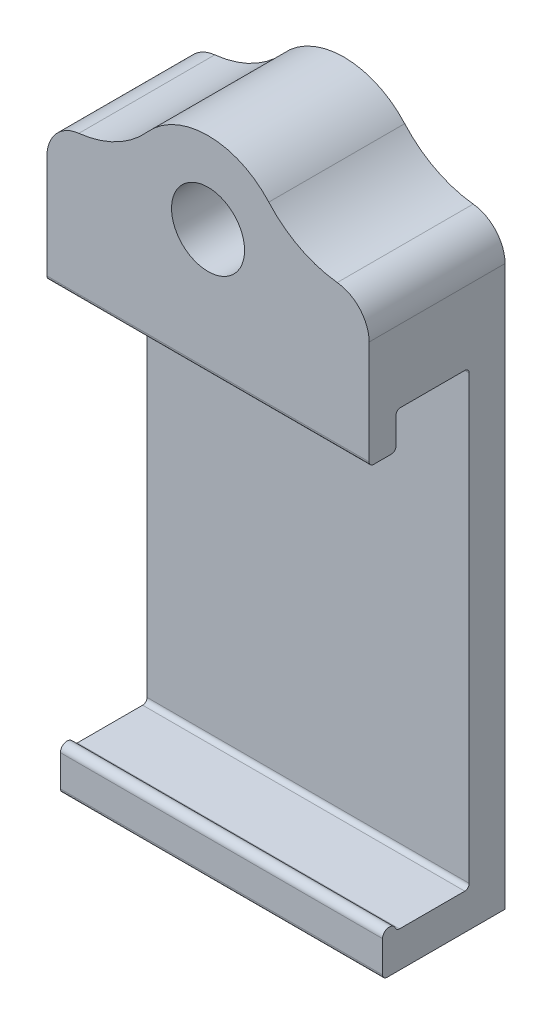
SolidWorks part; units mm, degrees
ref_plane "Front Plane" through (0, 0, 0) normal (0, 0, 1) x (1, 0, 0)
ref_plane "Top Plane" through (0, 0, 0) normal (0, 1, 0) x (1, 0, 0)
ref_plane "Right Plane" through (0, 0, 0) normal (1, 0, 0) x (0, 0, -1)
sketch "Sketch2" plane through (0, 0, 0) normal (1, 0, 0) x (0, 0, -1)
  line L0 (-3.25, 16.825) -> (-5.6312, 16.825)
  line L1 (-3.25, -20) -> (3.25, -20) construction
  line L2 (-3.25, -20) -> (-3.25, 20) construction
  line L3 (-3.25, 20) -> (3.25, 20) construction
  line L4 (3.25, -20) -> (3.25, 20) construction
  line L5 (-3.25, -20) -> (3.25, 20) construction
  line L6 (-3.25, 20) -> (3.25, -20) construction
  line L7 (-5.6312, 16.825) -> (-5.6312, 23.175)
  line L8 (-5.6312, 23.175) -> (6.425, 23.175)
  line L9 (6.425, 23.175) -> (6.425, -23.175)
  line L10 (6.425, -23.175) -> (-4.4406, -23.175)
  line L11 (-4.4406, -23.175) -> (-4.4406, -20)
  line L12 (-3.25, 16.825) -> (-3.25, 20)
  line L13 (-3.25, 20) -> (3.25, 20)
  line L14 (3.25, 20) -> (3.25, -20)
  line L15 (3.25, -20) -> (-3.25, -20)
  line L16 (-4.4406, -20) -> (-3.25, -20) construction
  line L17 (-5.6312, 23.175) -> (-3.25, 20) construction
  line L18 (3.25, 20) -> (6.425, 23.175) construction
  line L19 (3.25, -20) -> (6.425, -23.175) construction
  arc A0 (-3.25, -20) -> (-4.4406, -20) centre (-3.8453, -20) ccw
  point P0 (0, 0)
  dimension "D3" = 0.5953
  dimension "D1" = 40
  dimension "D2" = 6.5
  dimension "D4" = 3.175
  dimension "D5" = 2.3813
  dimension "D6" = 3.175
extrude "Boss-Extrude1" add sketch "Sketch2" along normal mid plane 28.575
sketch "Sketch3" plane through (0, 23.175, 0) normal (0, 1, 0) x (1, 0, 0)
  line L4 (-14.2875, 6.425) -> (-14.2875, -5.6312)
  line L5 (-14.2875, -5.6312) -> (14.2875, -5.6312)
  line L6 (14.2875, -5.6312) -> (14.2875, 6.425)
  line L7 (14.2875, 6.425) -> (-14.2875, 6.425)
  line L8 (-14.2875, 6.425) -> (-14.2875, -5.6312)
  line L9 (-14.2875, -5.6312) -> (14.2875, -5.6312)
  line L10 (14.2875, -5.6312) -> (14.2875, 6.425)
  line L11 (14.2875, 6.425) -> (-14.2875, 6.425)
  dimension "D1" = 0
extrude "Boss-Extrude2" add sketch "Sketch3" along normal blind 12.7
sketch "Sketch4" plane through (0, 0, 5.6312) normal (0, 0, 1) x (1, 0, 0)
  line L0 (-14.2875, 20) -> (14.2875, 35.875) construction
  circle A0 centre (0, 27.9375) radius 3.2385
  dimension "D1" = 6.477
extrude "Cut-Extrude1" cut sketch "Sketch4" against normal through all
fillet "Fillet1" radius 0.3969 7 edges at (0, 16.825, 3.25) (0, 16.825, 5.6312) (0, -23.175, 4.4406) (0, 20, -3.25) (0, 20, 3.25) (0, -20, -3.25) (0, -20, 3.25)
sketch "Sketch6" plane through (0, 0, 5.6312) normal (0, 0, 1) x (1, 0, 0)
  line L0 (-14.2875, 29.525) -> (-7.0302, 29.525)
  line L1 (-14.2875, 35.875) -> (-14.2875, 17.2219) construction
  line L2 (7.0302, 29.525) -> (14.2875, 29.525)
  line L3 (14.2875, 35.875) -> (14.2875, 17.2219) construction
  line L5 (-14.2875, 29.525) -> (-14.2875, 35.875)
  line L6 (-14.2875, 35.875) -> (14.2875, 35.875)
  line L7 (14.2875, 35.875) -> (14.2875, 29.525)
  arc A0 (7.0302, 29.525) -> (-7.0302, 29.525) centre (0, 27.9375) ccw
  circle A1 centre (0, 27.9375) radius 3.2385 construction
  point P1 (14.2875, 32.0678)
  dimension "D1" = 3.9688
  dimension "D2" = 6.35
extrude "Cut-Extrude2" cut sketch "Sketch6" against normal through all both and the other way through all
fillet "Fillet2" radius 9.525 2 edges at (7.0302, 29.525, -0.3969) (-7.0302, 29.525, -0.3969)
fillet "Fillet3" radius 3.175 2 edges at (14.2875, 29.525, -0.3969) (-14.2875, 29.525, -0.3969)
